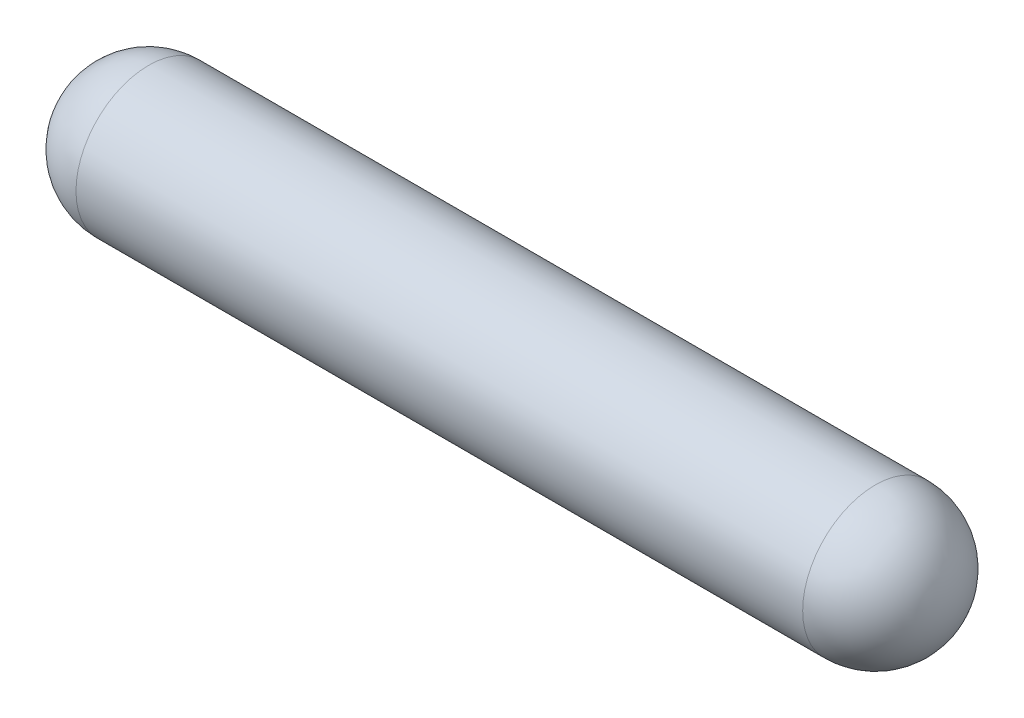
SolidWorks part; units mm, degrees
material "Alloy Steel"
ref_plane "Front Plane" through (0, 0, 0) normal (0, 0, 1) x (1, 0, 0)
ref_plane "Top Plane" through (0, 0, 0) normal (0, 1, 0) x (1, 0, 0)
ref_plane "Right Plane" through (0, 0, 0) normal (1, 0, 0) x (0, 0, -1)
sketch "Sketch1" plane through (0, 0, 0) normal (0, 0, 1) x (1, 0, 0)
  line L0 (0, 0) -> (9, 0) construction
  line L1 (-0.75, 0.75) -> (-8.25, 0.75)
  line L2 (0, 0) -> (-9, 0)
  arc A0 (-8.25, 0.75) -> (-9, 0) centre (-8.25, 0) ccw
  arc A1 (-0.75, 0.75) -> (0, 0) centre (-0.75, 0) cw
  dimension "D1" = 9
  dimension "D2" = 1.5
revolve "Revolve1" add sketch "Sketch1" angle 360 about L0
